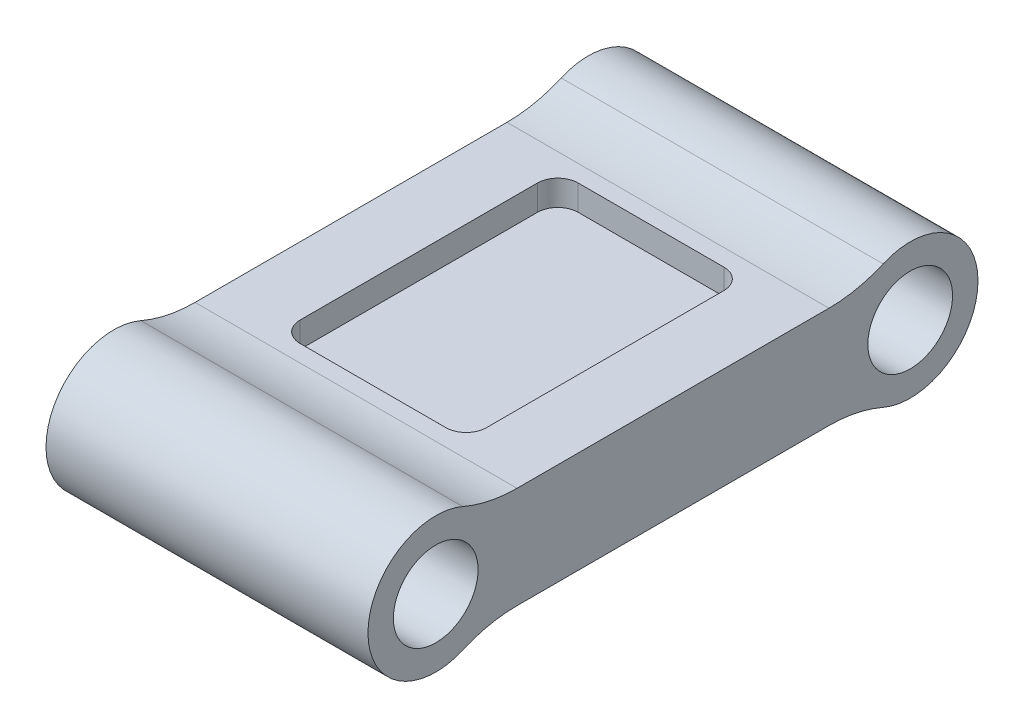
SolidWorks part; units mm, degrees
material "6061-T6 (SS)"
ref_plane "Front Plane" through (0, 0, 0) normal (0, 0, 1) x (1, 0, 0)
ref_plane "Top Plane" through (0, 0, 0) normal (0, 1, 0) x (1, 0, 0)
ref_plane "Right Plane" through (0, 0, 0) normal (1, 0, 0) x (0, 0, -1)
sketch "Sketch1" plane through (0, 0, 0) normal (1, 0, 0) x (0, 0, -1)
  line L0 (0, 0) -> (177.8, 0)
  line L1 (16.8005, -19.05) -> (160.9995, -19.05)
  line L2 (16.8005, 19.05) -> (160.9995, 19.05)
  line L3 (0, 19.05) -> (177.8, 19.05) construction
  line L4 (0, -19.05) -> (177.8, -19.05) construction
  circle A0 centre (0, 0) radius 15.875
  circle A1 centre (177.8, 0) radius 15.875
  circle A2 centre (0, 0) radius 25.4
  circle A3 centre (177.8, 0) radius 25.4
  dimension "D1" = 31.75
  dimension "D3" = 50.8
  dimension "D2" = 177.8
  dimension "D4" = 19.05
  dimension "D5" = 19.05
extrude "Boss-Extrude1" add sketch "Sketch1" along normal blind 127
fillet "Fillet1" radius 50.8 4 edges at (63.5, -19.05, -160.9995) (63.5, -19.05, -16.8005) (63.5, 19.05, -16.8005) (63.5, 19.05, -160.9995)
sketch "Sketch2" plane through (0, 19.05, 0) normal (0, 1, 0) x (1, 0, 0)
  line L0 (127, 30.4535) -> (127, 147.3465) construction
  line L1 (120.65, 210.2979) -> (146.05, 210.2979)
  line L2 (120.65, 210.2979) -> (120.65, -31.3917)
  line L3 (120.65, -31.3917) -> (146.05, -31.3917)
  line L4 (146.05, 210.2979) -> (146.05, -31.3917)
  dimension "D1" = 6.35
  dimension "D2" = 25.4
extrude "Cut-Extrude1" cut sketch "Sketch2" against normal through all and the other way through all
sketch "Sketch3" plane through (0, 19.05, 0) normal (0, 1, 0) x (1, 0, 0)
  line L0 (0, 30.4535) -> (0, 147.3465) construction
  line L1 (25.4, 140.9965) -> (95.25, 140.9965)
  line L2 (25.4, 140.9965) -> (25.4, 36.8035)
  line L3 (25.4, 36.8035) -> (95.25, 36.8035)
  line L4 (95.25, 140.9965) -> (95.25, 36.8035)
  line L5 (120.65, 147.3465) -> (120.65, 30.4535) construction
  line L6 (120.65, 147.3465) -> (0, 147.3465) construction
  line L7 (0, 30.4535) -> (120.65, 30.4535) construction
  dimension "D1" = 25.4
  dimension "D2" = 25.4
  dimension "D3" = 6.35
  dimension "D4" = 6.35
extrude "Cut-Extrude2" cut sketch "Sketch3" against normal blind 9.525
fillet "Fillet2" radius 7.62 4 edges at (25.4, 14.2875, -36.8035) (95.25, 14.2875, -36.8035) (25.4, 14.2875, -140.9965) (95.25, 14.2875, -140.9965)
ref_plane "Plane1" through (0, 0, 0) normal (0, 1, 0) x (1, 0, 0)
mirror "Mirror1" about plane through (0, 0, 0) normal (0, 1, 0) of "Fillet2", "Cut-Extrude2"
